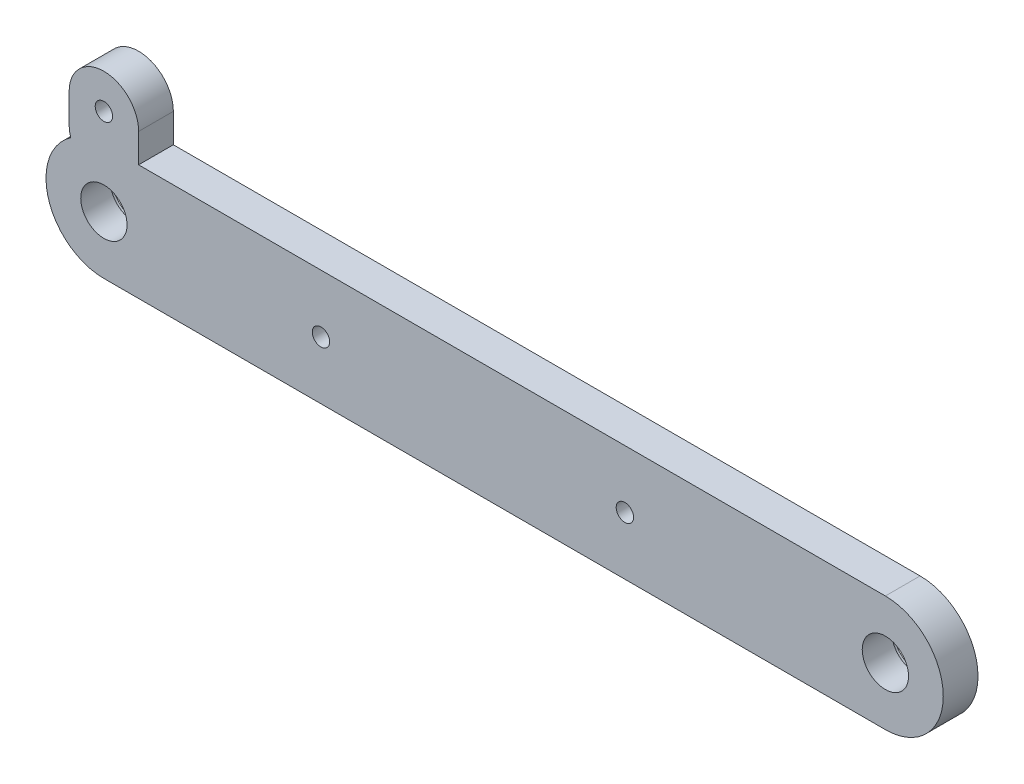
SolidWorks part; units mm, degrees
ref_plane "前视基准面" through (0, 0, 0) normal (0, 0, 1) x (1, 0, 0)
ref_plane "上视基准面" through (0, 0, 0) normal (0, 1, 0) x (1, 0, 0)
ref_plane "右视基准面" through (0, 0, 0) normal (1, 0, 0) x (0, 0, -1)
other "Configuration Table"
sketch "草图1" plane through (0, 0, 0) normal (0, 0, 1) x (1, 0, 0)
  line L3 (-8.9768, 0) -> (15.281, 0) construction
  line L4 (0, 0) -> (135, 0) construction
  line L5 (0, 10) -> (135, 10)
  line L6 (0, -10) -> (135, -10)
  line L7 (0, 0) -> (-60, 0) construction
  line L8 (0, -10) -> (-60, -10) construction
  line L9 (0, 10) -> (-60, 10) construction
  line L10 (0, 10) -> (0, 15) construction
  line L11 (-6, 10) -> (-6, 15)
  line L12 (6, 10) -> (6, 15)
  line L13 (67.5, 10) -> (135, 10)
  circle A3 centre (135, 0) radius 4
  circle A4 centre (0, 0) radius 4
  circle A5 centre (-60, 0) radius 4 construction
  arc A6 (0, 10) -> (0, -10) centre (0, 0) ccw
  arc A7 (135, -10) -> (135, 10) centre (135, 0) ccw
  arc A8 (0, -10) -> (0, 10) centre (0, 0) ccw construction
  arc A9 (-60, 10) -> (-60, -10) centre (-60, 0) ccw construction
  arc A10 (-6, 10) -> (6, 10) centre (0, 10) ccw
  arc A11 (6, 15) -> (-6, 15) centre (0, 15) ccw
  spline S0 degree 3 poles (-60, 10) (-41.0074, 16.4419) (-10.2231, 26.2095) (55.276, 16.4092) (99.7834, 10.1017) (135, 10) knots 0 0 0 0 0.312279 0.468288 1 1 1 1 construction
  point P9 (67.5, 0)
  point P15 (-30, 0)
  point P25 (0, 12.5)
  dimension "D3" = 8
  dimension "D4" = 8
  dimension "D5" = 8
  dimension "D6" = 10
  dimension "D7" = 10
  dimension "D8" = 6
  dimension "D1" = 135
  dimension "D2" = 60
  dimension "D9" = 5
extrude "凸台-拉伸1" add sketch "草图1" along normal blind 6 contours A10 A6 L6 A7 L5 A4 A3 | A6 A10 L5 | L12 A11 L11 A10 A6 L5 | A5
sketch "草图2" plane through (0, 0, 0) normal (0, 0, -1) x (-1, 0, 0)
  point P0 (-135, 0)
  point P6 (0, 0)
  point P12 (0, 0)
  point P13 (0, 0)
hole_wizard "M5 六角头螺栓的柱形沉头孔1" positions "草图2" profile "草图3" counterbore size "M5" standard "GB" end condition through all
sketch "草图3" plane through (135, 0, 0) normal (1, 0, 0) x (0, 1, 0)
  line L0 (0, 0) -> (0, 6)
  line L1 (0, 6) -> (4, 6)
  line L3 (4, 6) -> (4, 0.9)
  line L4 (4, 0.9) -> (4.75, 0.9)
  line L5 (4.75, 0.9) -> (4.75, 0)
  line L7 (4.75, 0) -> (0, 0)
  line L11 (0, -6.35) -> (0, 107.95) construction
  dimension "通孔孔直径" = 8
  dimension "通孔孔深度" = 6
  dimension "柱形沉头孔直径" = 9.5
  dimension "柱形沉头孔深度" = 0.9
sketch "草图7" plane through (0, 0, 0) normal (0, 0, -1) x (-1, 0, 0)
  line L0 (-135, 0) -> (60, 0) construction
  circle A0 centre (-37.5, 0) radius 1.5
  circle A1 centre (-90, 0) radius 1.5
  circle A3 centre (0, 15) radius 1.5
  point P19 (-135, 0)
  dimension "D1" = 3
  dimension "D2" = 3
  dimension "D3" = 37.5
  dimension "D6" = 3
  dimension "D5" = 90
extrude "切除-拉伸1" cut sketch "草图7" against normal through all both and the other way through all
